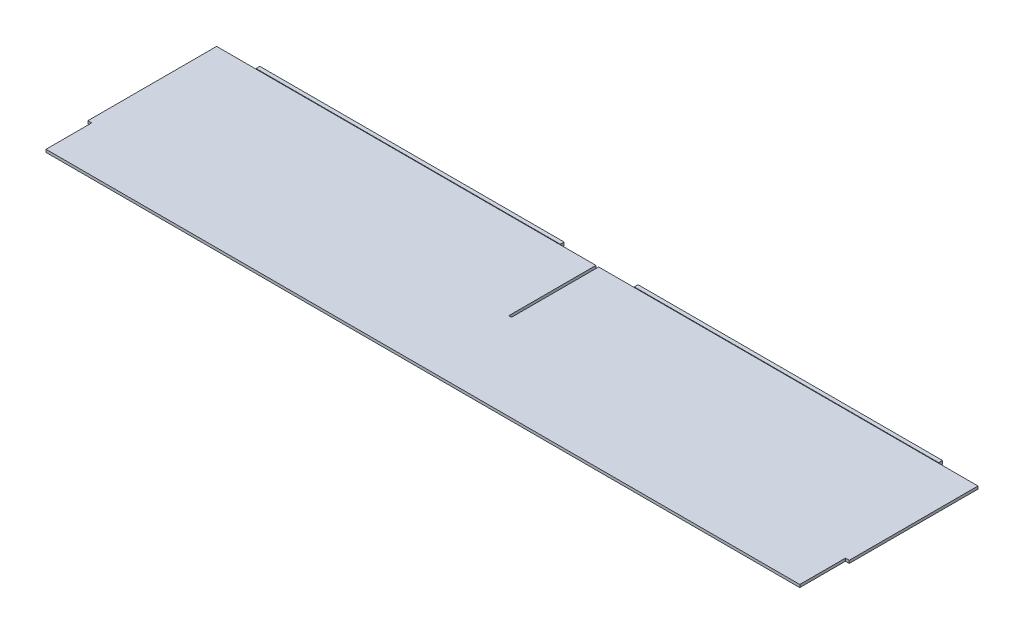
SolidWorks part; units mm, degrees
material "6061-T6 (SS)"
ref_plane "X-Y Datum" through (0, 0, 0) normal (0, 0, 1) x (1, 0, 0)
ref_plane "X-Z Datum" through (0, 0, 0) normal (0, 1, 0) x (1, 0, 0)
ref_plane "Y-Z Datum" through (0, 0, 0) normal (1, 0, 0) x (0, 0, -1)
sketch "Sketch1" plane through (0, 0, 0) normal (0, 1, 0) x (1, 0, 0)
  line L1 (-317.6778, 72.771) -> (317.6778, 72.771)
  line L2 (-317.6778, 72.771) -> (-317.6778, -72.771)
  line L3 (-317.6778, -72.771) -> (317.6778, -72.771)
  line L4 (317.6778, 72.771) -> (317.6778, -72.771)
  line L5 (-317.6778, 72.771) -> (317.6778, -72.771) construction
  line L6 (-317.6778, -72.771) -> (317.6778, 72.771) construction
  point P0 (0, 0)
  dimension "D1" = 635.3556
  dimension "D2" = 145.542
extrude "Boss-Extrude1" add sketch "Sketch1" along normal mid plane 2.286
sketch "Sketch2" plane through (0, 0, -72.771) normal (0, 0, -1) x (-1, 0, 0)
  line L20 (-317.6778, -1.143) -> (317.6778, -1.143) construction
  line L21 (-284.8229, -1.143) -> (-30.8229, -1.143)
  line L22 (30.8229, -1.143) -> (284.8229, -1.143)
  line L40 (30.8229, -1.143) -> (30.8229, 1.5875)
  line L41 (30.8229, 1.5875) -> (284.8229, 1.5875)
  line L42 (284.8229, 1.5875) -> (284.8229, -1.143)
  line L56 (-284.8229, -1.143) -> (-284.8229, 1.5875)
  line L57 (-284.8229, 1.5875) -> (-30.8229, 1.5875)
  line L58 (-30.8229, 1.5875) -> (-30.8229, -1.143)
extrude "Boss-Extrude2" add sketch "Sketch2" along normal blind 3.175
sketch "Sketch3" plane through (0, -1.143, 0) normal (0, -1, 0) x (1, 0, 0)
  line L1 (-317.6778, 72.771) -> (-314.5028, 72.771)
  line L2 (-317.6778, 72.771) -> (-317.6778, 34.671)
  line L3 (-317.6778, 34.671) -> (-314.5028, 34.671)
  line L4 (-314.5028, 72.771) -> (-314.5028, 34.671)
  dimension "D1" = 38.1
  dimension "D2" = 3.175
extrude "Cut-Extrude1" cut sketch "Sketch3" against normal through all
mirror "Mirror1" about plane through (0, 0, 0) normal (1, 0, 0) of "Cut-Extrude1"
sketch "Sketch4" plane through (0, -1.143, 0) normal (0, -1, 0) x (1, 0, 0)
  line L0 (30.8229, -72.771) -> (-30.8229, -72.771) construction
  line L1 (-1.143, -72.771) -> (1.143, -72.771)
  line L2 (-1.143, -72.771) -> (-1.143, 0)
  line L3 (-1.143, 0) -> (1.143, 0)
  line L4 (1.143, -72.771) -> (1.143, 0)
  line L5 (-1.143, -75.946) -> (-1.143, -72.771) construction
  dimension "D1" = 72.771
  dimension "D2" = 2.286
extrude "Cut-Extrude2" cut sketch "Sketch4" against normal through all
